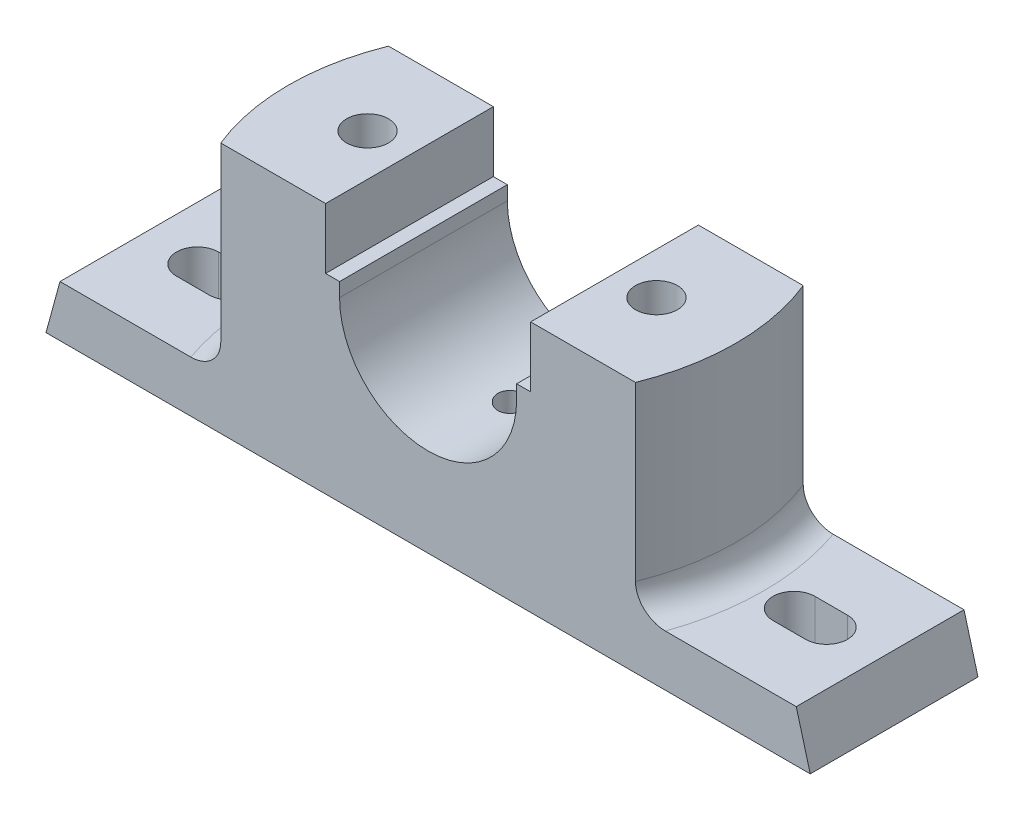
SolidWorks part; units mm, degrees
ref_plane "Front Plane" through (0, 0, 0) normal (0, 0, 1) x (1, 0, 0)
ref_plane "Top Plane" through (0, 0, 0) normal (0, 1, 0) x (1, 0, 0)
ref_plane "Right Plane" through (0, 0, 0) normal (1, 0, 0) x (0, 0, -1)
sketch "Sketch1" plane through (0, 0, 0) normal (0, 0, 1) x (1, 0, 0)
  line L0 (0, -18.2775) -> (0, -47.2775) construction
  line L1 (82, 0) -> (-82, 0)
  line L2 (-82, 0) -> (-79, 11)
  line L3 (-79, 11) -> (-49, 11)
  line L4 (-49, 11) -> (-49, 54)
  line L5 (-49, 54) -> (-22, 54)
  line L6 (-22, 54) -> (-22, 41)
  line L7 (-22, 41) -> (-19, 41)
  line L8 (-19, 41) -> (-19, 38)
  line L9 (19, 41) -> (19, 38)
  line L10 (22, 41) -> (19, 41)
  line L11 (22, 54) -> (22, 41)
  line L12 (49, 54) -> (22, 54)
  line L13 (49, 11) -> (49, 54)
  line L14 (79, 11) -> (49, 11)
  line L15 (82, 0) -> (79, 11)
  arc A0 (-19, 38) -> (19, 38) centre (0, 38) ccw
  point P20 (0, 0)
  dimension "D8" = 19
  dimension "D1" = 164
  dimension "D2" = 3
  dimension "D3" = 11
  dimension "D4" = 54
  dimension "D5" = 49
  dimension "D6" = 13
  dimension "D7" = 16
  dimension "D9" = 44
extrude "Boss-Extrude1" add sketch "Sketch1" along normal mid plane 36
sketch "Sketch3" plane through (0, 54, 0) normal (0, 1, 0) x (1, 0, 0)
  line L0 (-22, 18) -> (-49, 18) construction
  line L1 (-22, -18) -> (-49, -18) construction
  line L2 (-49, -18) -> (-49, 18) construction
  line L3 (-44.4972, 18) -> (-49, 18)
  line L4 (-44.4972, -18) -> (-49, -18)
  line L5 (-49, -18) -> (-49, 18)
  line L6 (0, 31.016) -> (0, -35.9065) construction
  line L7 (49, -18) -> (49, 18)
  line L8 (44.4972, -18) -> (49, -18)
  line L9 (44.4972, 18) -> (49, 18)
  arc A0 (-44.4972, 18) -> (-44.4972, -18) centre (0, 0) ccw
  arc A1 (44.4972, 18) -> (44.4972, -18) centre (0, 0) cw
  dimension "D1" = 48
extrude "Cut-Extrude1" cut sketch "Sketch3" against normal up to surface (43 mm away) up to face at (-64, 11, 0)
sketch "Sketch12" plane through (0, 0, 0) normal (0, -1, 0) x (1, 0, 0)
  line L0 (0, 25.6662) -> (0, -24.6604) construction
  line L1 (-41, 10) -> (-21, 10)
  line L2 (-41, 10) -> (-41, -10)
  line L3 (-41, -10) -> (-21, -10)
  line L4 (-21, 10) -> (-21, -10)
  line L5 (-41, 10) -> (-21, -10) construction
  line L6 (-41, -10) -> (-21, 10) construction
  line L7 (41, -10) -> (21, 10) construction
  line L8 (41, 10) -> (21, -10) construction
  line L9 (21, 10) -> (21, -10)
  line L10 (41, -10) -> (21, -10)
  line L11 (41, 10) -> (41, -10)
  line L12 (41, 10) -> (21, 10)
  point P0 (-31, 0)
  point P12 (31, 0)
  dimension "D1" = 20
  dimension "D2" = 62
extrude "Cut-Extrude2" cut sketch "Sketch12" against normal blind 8
sketch "Sketch13" plane through (0, 54, 0) normal (0, 1, 0) x (1, 0, 0)
  line L0 (0, 18) -> (0, -18) construction
  line L1 (19, 18) -> (-19, 18) construction
  line L2 (-19, -18) -> (19, -18) construction
  circle A0 centre (-31, 0) radius 4.5
  circle A1 centre (31, 0) radius 4.5
  dimension "D2" = 9
  dimension "D1" = 62
extrude "Cut-Extrude3" cut sketch "Sketch13" against normal through all
sketch "Sketch14" plane through (0, 11, 0) normal (0, 1, 0) x (1, 0, 0)
  line L0 (0, 18) -> (0, -18) construction
  line L1 (19, 18) -> (-19, 18) construction
  line L2 (-19, -18) -> (19, -18) construction
  line L3 (-67.5, 0) -> (-60.5, 0) construction
  line L4 (-67.5, 4.5) -> (-60.5, 4.5)
  line L5 (-67.5, -4.5) -> (-60.5, -4.5)
  line L6 (67.5, 0) -> (60.5, 0) construction
  line L7 (67.5, 4.5) -> (60.5, 4.5)
  line L8 (67.5, -4.5) -> (60.5, -4.5)
  arc A0 (-67.5, 4.5) -> (-67.5, -4.5) centre (-67.5, 0) ccw
  arc A1 (-60.5, -4.5) -> (-60.5, 4.5) centre (-60.5, 0) ccw
  arc A2 (67.5, 4.5) -> (67.5, -4.5) centre (67.5, 0) cw
  arc A3 (60.5, -4.5) -> (60.5, 4.5) centre (60.5, 0) cw
  point P8 (-64, 0)
  point P16 (64, 0)
  dimension "D1" = 4.5
  dimension "D2" = 7
  dimension "D3" = 128
extrude "Cut-Extrude4" cut sketch "Sketch14" against normal through all
ref_plane "Plane1" through (0, 19, 0) normal (0, 1, 0) x (1, 0, 0)
sketch "Sketch18" plane through (0, 19, 0) normal (0, 1, 0) x (1, 0, 0)
  circle A0 centre (0, 0) radius 3
  dimension "D1" = 6
extrude "Cut-Extrude8" cut sketch "Sketch18" against normal blind 6 and the other way up to next
fillet "Fillet1" radius 6 2 edges at (48, 11, 0) (-48, 11, 0)
